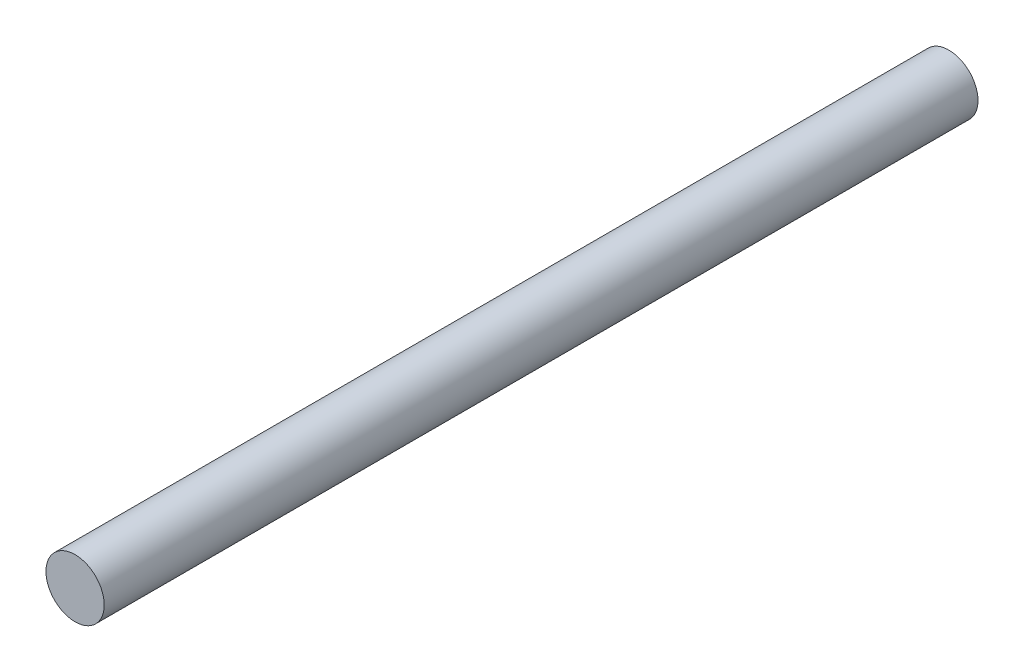
SolidWorks part; units mm, degrees
ref_plane "Front" through (0, 0, 0) normal (0, 0, 1) x (1, 0, 0)
ref_plane "Top" through (0, 0, 0) normal (0, 1, 0) x (1, 0, 0)
ref_plane "Right" through (0, 0, 0) normal (1, 0, 0) x (0, 0, -1)
sketch "Esquisse1" plane through (0, 0, 0) normal (0, 0, 1) x (1, 0, 0)
  circle A0 centre (0, 0) radius 3
  dimension "D1" = 6
extrude "Boss.-Extru.1" add sketch "Esquisse1" along normal blind 90
